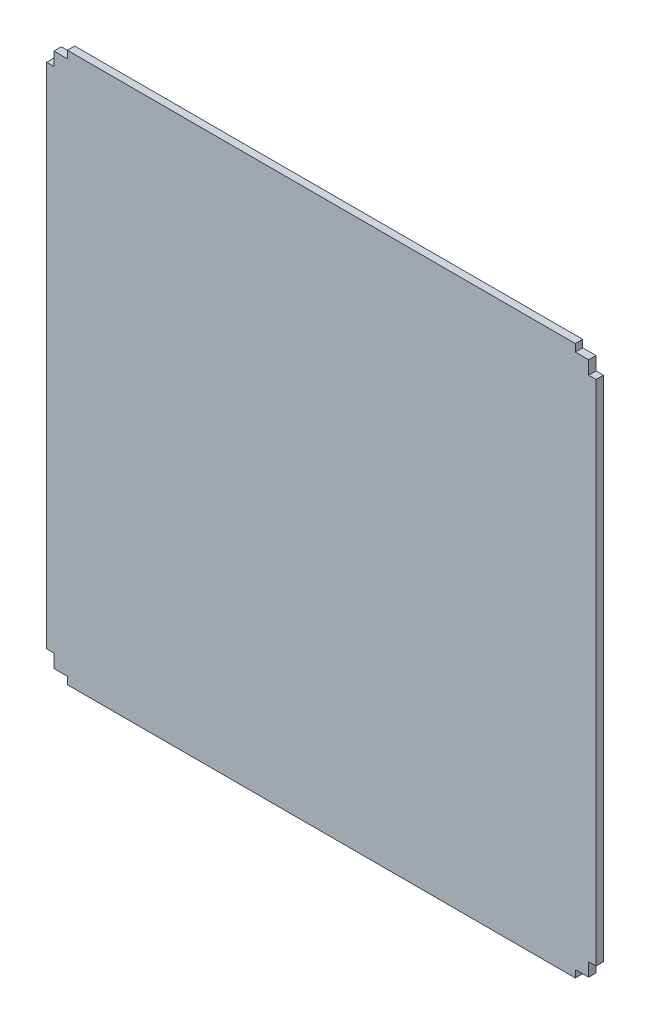
SolidWorks part; units mm, degrees
ref_plane "前视基准面" through (0, 0, 0) normal (0, 0, 1) x (1, 0, 0)
ref_plane "上视基准面" through (0, 0, 0) normal (0, 1, 0) x (1, 0, 0)
ref_plane "右视基准面" through (0, 0, 0) normal (1, 0, 0) x (0, 0, -1)
sketch "草图1" plane through (0, 0, 0) normal (0, 0, 1) x (1, 0, 0)
  line L0 (0, 0) -> (5, 0)
  line L2 (0, 0) -> (0, 5)
  line L3 (0, 200) -> (5, 200)
  line L4 (200, 0) -> (200, 5)
  line L5 (5, 0) -> (5, -2.75)
  line L6 (200, 0) -> (195, 0)
  line L7 (195, 0) -> (195, -2.75)
  line L8 (195, -2.75) -> (5, -2.75)
  line L10 (200, 5) -> (202.75, 5)
  line L11 (202.75, 5) -> (202.75, 195)
  line L12 (202.75, 195) -> (200, 195)
  line L13 (200, 200) -> (195, 200)
  line L15 (195, 200) -> (195, 202.75)
  line L16 (195, 202.75) -> (5, 202.75)
  line L17 (5, 202.75) -> (5, 200)
  line L19 (0, 200) -> (0, 195)
  line L20 (0, 195) -> (-2.75, 195)
  line L21 (-2.75, 195) -> (-2.75, 5)
  line L22 (-2.75, 5) -> (0, 5)
  line L25 (200, 195) -> (200, 200)
extrude "凸台-拉伸1" add sketch "草图1" along normal blind 2.75
